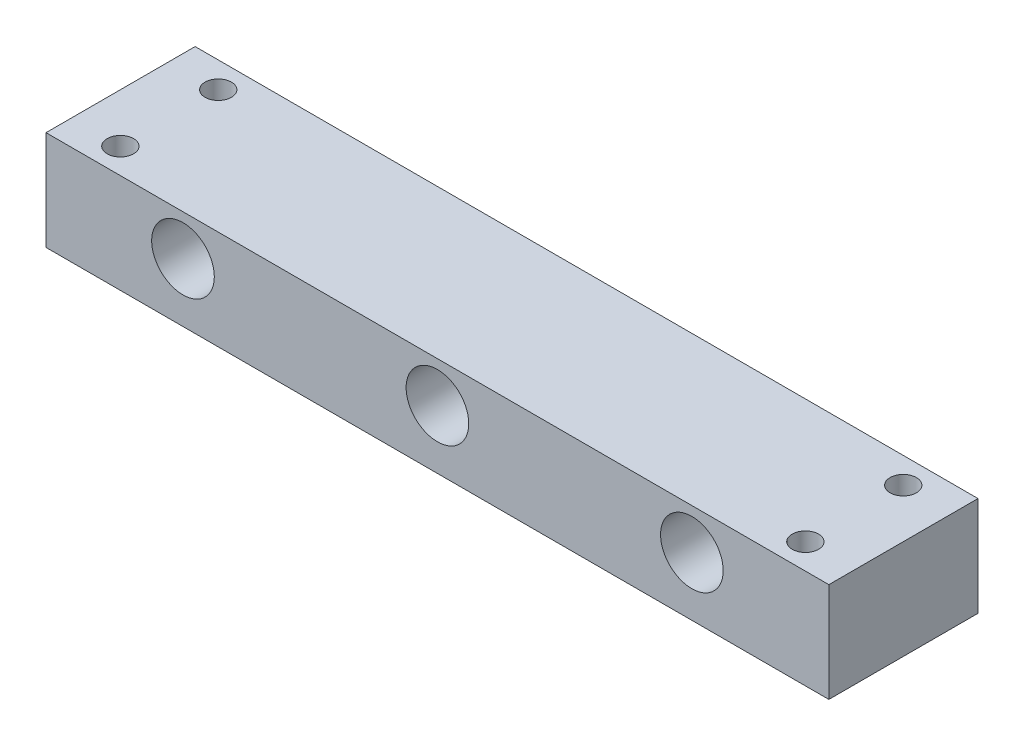
SolidWorks part; units mm, degrees
ref_plane "Front Plane" through (0, 0, 0) normal (0, 0, 1) x (1, 0, 0)
ref_plane "Top Plane" through (0, 0, 0) normal (0, 1, 0) x (1, 0, 0)
ref_plane "Right Plane" through (0, 0, 0) normal (1, 0, 0) x (0, 0, -1)
sketch "Sketch1" plane through (0, 0, 0) normal (0, 1, 0) x (1, 0, 0)
  line L1 (0, 0) -> (400, 0)
  line L2 (0, 0) -> (0, 76.2)
  line L3 (0, 76.2) -> (400, 76.2)
  line L4 (400, 0) -> (400, 76.2)
  dimension "D1" = 76.2
  dimension "D2" = 400
extrude "Boss-Extrude1" add sketch "Sketch1" along normal blind 50.8
sketch "Sketch3" plane through (0, 50.8, 0) normal (0, 1, 0) x (1, 0, 0)
  line L1 (0, 0) -> (200, 0)
  line L2 (0, 0) -> (0, 38)
  line L3 (0, 38) -> (200, 38)
  line L4 (200, 0) -> (200, 38)
  line L5 (25, 63) -> (375, 63)
  line L6 (25, 63) -> (25, 13)
  line L7 (25, 13) -> (375, 13)
  line L8 (375, 63) -> (375, 13)
  line L9 (25, 63) -> (375, 13) construction
  line L10 (25, 13) -> (375, 63) construction
  circle A0 centre (25, 63) radius 6.75
  circle A1 centre (25, 13) radius 6.75
  circle A2 centre (375, 63) radius 6.75
  circle A3 centre (375, 13) radius 6.75
  dimension "D1" = 200
  dimension "D2" = 38
  dimension "D3" = 350
  dimension "D4" = 50
extrude "Cut-Extrude2" cut sketch "Sketch3" against normal blind 50.8 contours A2 | A1 | A3 | A0
sketch "Sketch5" plane through (0, 0, 0) normal (0, 0, 1) x (1, 0, 0)
  line L0 (200, 30) -> (330, 30)
  line L1 (0, 0) -> (200, 0)
  line L2 (0, 0) -> (0, 30)
  line L4 (200, 0) -> (200, 30)
  line L5 (200, 30) -> (70, 30)
  circle A0 centre (200, 30) radius 16
  circle A1 centre (70, 30) radius 16
  circle A2 centre (330, 30) radius 16
  dimension "D3" = 130
  dimension "D1" = 30
  dimension "D2" = 200
  dimension "D4" = 130
extrude "Cut-Extrude3" cut sketch "Sketch5" against normal through all
